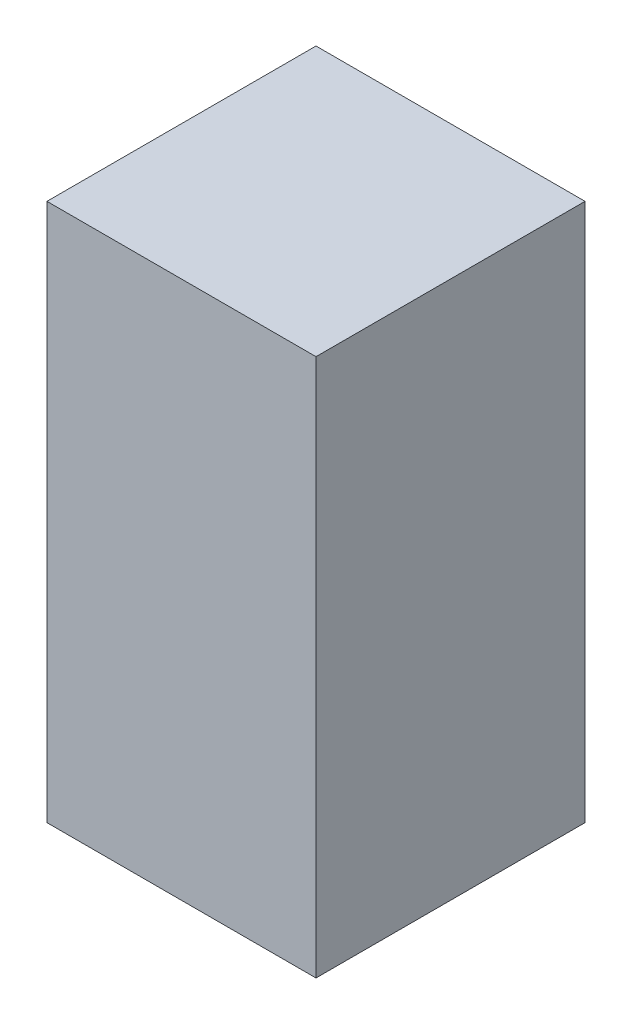
SolidWorks part; units mm, degrees
ref_plane "Front Plane" through (0, 0, 0) normal (0, 0, 1) x (1, 0, 0)
ref_plane "Top Plane" through (0, 0, 0) normal (0, 1, 0) x (1, 0, 0)
ref_plane "Right Plane" through (0, 0, 0) normal (1, 0, 0) x (0, 0, -1)
sketch "Sketch1" plane through (0, 0, 0) normal (0, 1, 0) x (1, 0, 0)
  line L1 (-12.7, -12.7) -> (12.7, -12.7)
  line L2 (-12.7, -12.7) -> (-12.7, 12.7)
  line L3 (-12.7, 12.7) -> (12.7, 12.7)
  line L4 (12.7, -12.7) -> (12.7, 12.7)
  line L5 (-12.7, -12.7) -> (12.7, 12.7) construction
  line L6 (-12.7, 12.7) -> (12.7, -12.7) construction
  point P0 (0, 0)
  dimension "D1" = 25.4
extrude "Boss-Extrude1" add sketch "Sketch1" along normal blind 50.8
